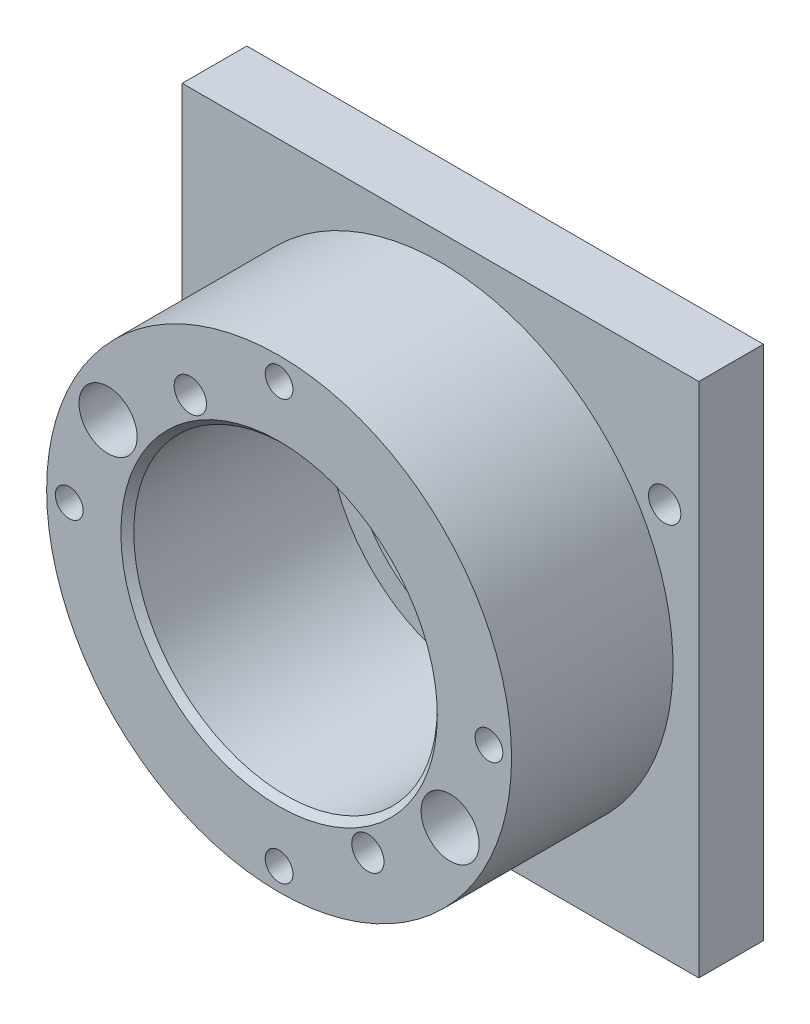
SolidWorks part; units mm, degrees
ref_plane "Ebene vorne" through (0, 0, 0) normal (0, 0, 1) x (1, 0, 0)
ref_plane "Ebene oben" through (0, 0, 0) normal (0, 1, 0) x (1, 0, 0)
ref_plane "Ebene rechts" through (0, 0, 0) normal (1, 0, 0) x (0, 0, -1)
sketch "Skizze1" plane through (0, 0, 0) normal (0, 0, 1) x (1, 0, 0)
  line L0 (20.859, 34.7153) -> (-20.859, -34.7153)
  line L1 (-40, -40) -> (40, -40)
  line L2 (-40, -40) -> (-40, 40)
  line L3 (-40, 40) -> (40, 40)
  line L4 (40, -40) -> (40, 40)
  line L5 (-40, -40) -> (40, 40) construction
  line L6 (-40, 40) -> (40, -40) construction
  line L7 (-14.0841, 26.4884) -> (14.0841, -26.4884)
  line L8 (-23.8157, 13.75) -> (23.8157, -13.75)
  line L9 (0, 40) -> (0, 0) construction
  circle A0 centre (0, 0) radius 40.5
  circle A1 centre (0, 0) radius 30
  circle A2 centre (0, 0) radius 27.5
  point P0 (0, 0)
  dimension "D3" = 81
  dimension "D4" = 60
  dimension "D5" = 55
  dimension "D1" = 80
  dimension "D2" = 80
  dimension "D6" = 31
  dimension "D7" = 28
  dimension "D8" = 60
extrude "Aufsatz-Linear austragen1" add sketch "Skizze1" along normal blind 10 contours L3 L4 L1 L2
sketch "Skizze4" plane through (0, 0, 0) normal (0, 0, -1) x (-1, 0, 0)
  line L1 (34.7153, -20.859) -> (-34.7153, 20.859)
  line L2 (26.4884, 14.0841) -> (-26.4884, -14.0841)
  line L3 (-13.75, -23.8157) -> (13.75, 23.8157)
  line L5 (0, 0) -> (-46.9825, 0) construction
  line L6 (0, 0) -> (0, 54.5709) construction
  circle A0 centre (0, 0) radius 40.5
  circle A1 centre (0, 0) radius 30
  circle A2 centre (0, 0) radius 27.5
  dimension "D1" = 81
  dimension "D2" = 60
  dimension "D3" = 55
  dimension "D4" = 31
  dimension "D5" = 28
  dimension "D6" = 60
sketch "Skizze16" plane through (0, 0, 10) normal (0, 0, 1) x (1, 0, 0)
  circle A0 centre (0, 0) radius 20.1
  dimension "D1" = 40.2
extrude "Schnitt-Linear austragen1" cut sketch "Skizze16" against normal through all
sketch "Skizze17" plane through (0, 0, 10) normal (0, 0, 1) x (1, 0, 0)
  circle A0 centre (0, 0) radius 23.5
  circle A1 centre (0, 0) radius 36
  dimension "D1" = 72
  dimension "D2" = 47
extrude "Aufsatz-Linear austragen2" add sketch "Skizze17" along normal blind 25
sketch "Skizze18" plane through (0, 0, 35) normal (0, 0, 1) x (1, 0, 0)
  line L0 (0, 0) -> (0, 32.5)
  circle A0 centre (0, 0) radius 32.5
  dimension "D1" = 65
hole_wizard "Ø4.3 (4.3) Durchmesser Bohrung1" positions "Skizze20" profile "Skizze21" hole size "Ø4.3" standard "ANSI Metrisch"
sketch "Skizze20" plane through (0, 0, 35) normal (0, 0, 1) x (1, 0, 0)
  point P0 (0, 32.5)
sketch "Skizze21" plane through (0, 32.5, 35) normal (1, 0, 0) x (0, -1, 0)
  line L0 (0, 0) -> (0, 16.2919)
  line L1 (0, 16.2919) -> (2.15, 15)
  line L2 (2.15, 15) -> (2.15, 0)
  line L5 (2.15, 0) -> (0, 0)
  line L10 (0, 16.2919) -> (-2.15, 15) construction
  line L11 (0, -6.35) -> (0, 107.95) construction
  dimension "Bohrerdurchmesser" = 4.3
  dimension "Bohrungstiefe" = 15
  dimension "Spitzenwinkel" = 118
pattern_circular "Kreismuster1" count 4 over 360 about axis through (0, 0, 0) along (0, 0, 1) of "Ø4.3 (4.3) Durchmesser Bohrung1"
chamfer "Fase1" distance 1 angle 45 1 edges at (23.5, 0, 35)
hole_wizard "Ø5.0 (5) Durchmesser Bohrung1" positions "Skizze25" profile "Skizze26" hole size "Ø5.0" standard "ANSI Metrisch" end condition through all
sketch "Skizze25" plane through (0, 0, 0) normal (0, 0, -1) x (-1, 0, 0)
  point P0 (34.7153, -20.859)
  point P3 (-13.75, -23.8157)
  point P6 (13.75, 23.8157)
  point P9 (-34.7153, 20.859)
sketch "Skizze26" plane through (-34.7153, -20.859, 0) normal (1, 0, 0) x (0, 1, 0)
  line L0 (0, 0) -> (0, 35)
  line L1 (0, 35) -> (2.5, 35)
  line L2 (2.5, 35) -> (2.5, 0)
  line L5 (2.5, 0) -> (0, 0)
  line L11 (0, -6.35) -> (0, 107.95) construction
  dimension "Bohrerdurchmesser" = 5
  dimension "Bohrungstiefe" = 35
sketch "Skizze32" plane through (0, 0, 35) normal (0, 0, 1) x (1, 0, 0)
  line L0 (0, 0) -> (-26.4884, 14.0841)
  line L2 (-26.4884, 14.0841) -> (26.4884, -14.0841)
  line L4 (0, 0) -> (46.9825, 0) construction
  circle A0 centre (0, 0) radius 30
  dimension "D1" = 60
  dimension "D2" = 28
hole_wizard "Stirnsenkung für M5 Zylinderschraube mit Innensechskant1" positions "Skizze34" profile "Skizze35" counterbore size "M5" standard "ANSI Metrisch" end condition through all
sketch "Skizze34" plane through (0, 0, 35) normal (0, 0, 1) x (1, 0, 0)
  point P0 (-26.4884, 14.0841)
  point P3 (26.4884, -14.0841)
sketch "Skizze35" plane through (-26.4884, 14.0841, 35) normal (1, 0, 0) x (0, -1, 0)
  line L0 (0, 0) -> (0, 35)
  line L1 (0, 35) -> (2.5, 35)
  line L3 (2.5, 35) -> (2.5, 7)
  line L4 (2.5, 7) -> (4.5, 7)
  line L5 (4.5, 7) -> (4.5, 0)
  line L7 (4.5, 0) -> (0, 0)
  line L11 (0, -6.35) -> (0, 107.95) construction
  dimension "Bohrerdurchmesser" = 5
  dimension "Bohrungstiefe" = 35
  dimension "Senkdurchmesser2" = 9
  dimension "Senktiefe2" = 7
sketch "Skizze39" plane through (0, 0, 10) normal (0, 0, 1) x (1, 0, 0)
  circle A0 centre (0, 0) radius 20.1
  circle A1 centre (0, 0) radius 23.5
extrude "Schnitt-Linear austragen2" cut sketch "Skizze39" against normal blind 6
sketch "Skizze40" plane through (0, 0, 0) normal (0, 0, -1) x (-1, 0, 0)
  circle A0 centre (0, 0) radius 22
  circle A1 centre (0, 0) radius 24
  dimension "D1" = 44
  dimension "D2" = 48
extrude "Schnitt-Linear austragen3" cut sketch "Skizze40" against normal blind 2
sketch "Skizze41" plane through (0, 0, 2) normal (0, 0, -1) x (-1, 0, 0)
  line L0 (22.2516, -8.9925) -> (21.169, -8.9925)
  line L1 (22.2516, 9.0075) -> (21.169, 9.0075)
  line L2 (24.003, 0.0075) -> (23.0021, 0.0075) construction
  arc A0 (22.2516, -8.9925) -> (22.2516, 9.0075) centre (0.003, 0.0075) ccw
  circle A1 centre (0, 0) radius 24 construction
  arc A2 (21.169, -8.9925) -> (21.169, 9.0075) centre (0.003, 0.0075) ccw
  dimension "D2" = 18
  dimension "D4" = 23
  dimension "D3" = 24
  dimension "D1" = 18
extrude "Aufsatz-Linear austragen3" add sketch "Skizze41" along normal up to surface (2 mm away) up to face at (-24, 0, 0)
sketch "Skizze42" plane through (0, 0, 0) normal (0, 0, -1) x (-1, 0, 0)
  line L0 (21.4314, -8.3052) -> (21.169, -8.9925)
  line L1 (21.169, -8.9925) -> (21.3245, -8.9925)
  line L2 (22.2516, -8.9925) -> (21.169, -8.9925) construction
  line L3 (21.4314, -8.3052) -> (21.788, -8.3052)
  line L4 (21.7821, 8.3198) -> (21.4314, 8.3198)
  line L5 (21.4314, 8.3198) -> (21.169, 9.0075)
  line L6 (21.169, 9.0075) -> (21.3187, 9.0075)
  line L7 (22.2456, 9.0075) -> (21.169, 9.0075) construction
  arc A0 (21.3245, -8.9925) -> (21.788, -8.3052) centre (21.788, -8.8052) ccw
  arc A1 (21.7821, 8.3198) -> (21.3187, 9.0075) centre (21.7821, 8.8198) ccw
  arc A3 (22.2456, 9.0075) -> (22.2516, -8.9925) centre (0, 0) ccw construction
  dimension "D1" = 1
  dimension "D2" = 1
extrude "Schnitt-Linear austragen4" cut sketch "Skizze42" against normal up to surface (2 mm away) up to face at (-10.6052, 0.0036, 2)
